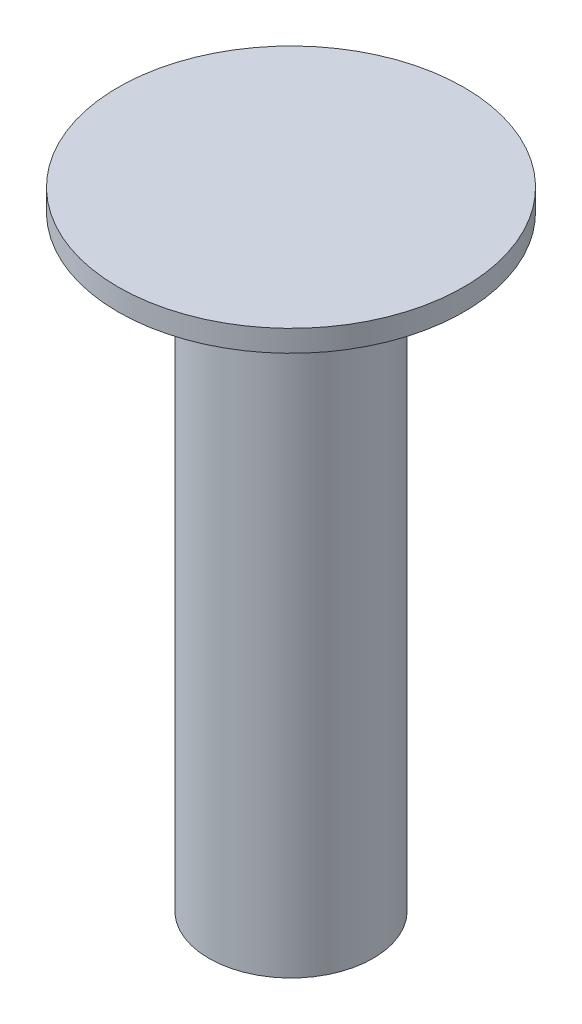
SolidWorks part; units mm, degrees
ref_plane "Alzado" through (0, 0, 0) normal (0, 0, 1) x (1, 0, 0)
ref_plane "Planta" through (0, 0, 0) normal (0, 1, 0) x (1, 0, 0)
ref_plane "Vista lateral" through (0, 0, 0) normal (1, 0, 0) x (0, 0, -1)
sketch "Croquis1" plane through (0, 0, 0) normal (0, 1, 0) x (1, 0, 0)
  circle A0 centre (0, 0) radius 3.8
  dimension "D1" = 7.6
extrude "Saliente-Extruir1" add sketch "Croquis1" along normal mid plane 28
sketch "Croquis2" plane through (0, 14, 0) normal (0, 1, 0) x (1, 0, 0)
  circle A0 centre (0, 0) radius 8
  dimension "D1" = 16
extrude "Saliente-Extruir2" add sketch "Croquis2" along normal blind 1
